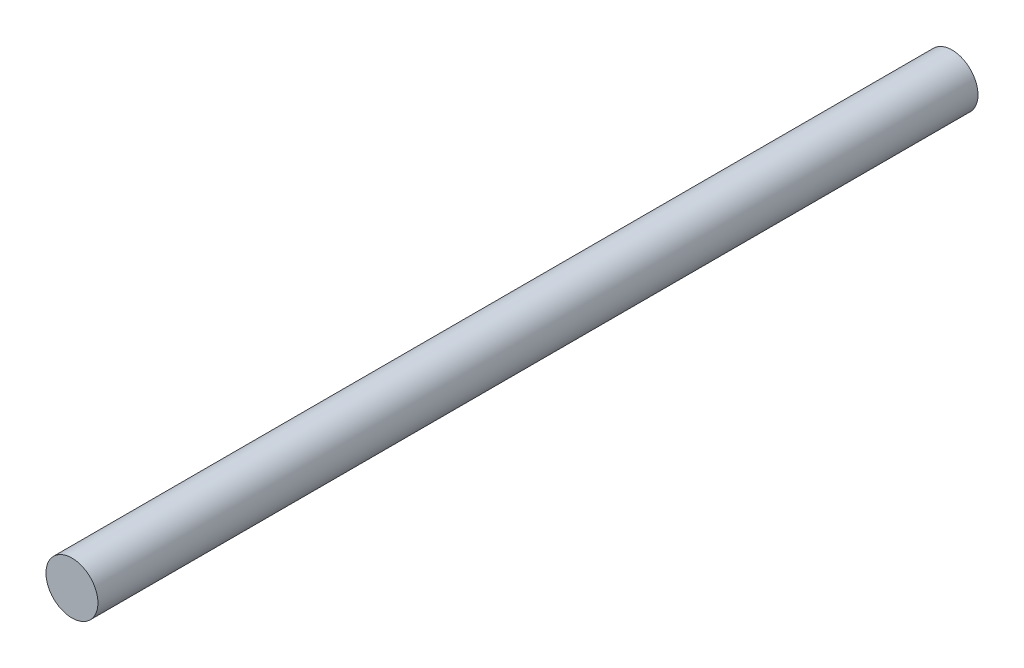
SolidWorks part; units mm, degrees
ref_plane "Front Plane" through (0, 0, 0) normal (0, 0, 1) x (1, 0, 0)
ref_plane "Top Plane" through (0, 0, 0) normal (0, 1, 0) x (1, 0, 0)
ref_plane "Right Plane" through (0, 0, 0) normal (1, 0, 0) x (0, 0, -1)
sketch "Sketch2" plane through (0, 0, 0) normal (0, 0, 1) x (1, 0, 0)
  circle A0 centre (0, 0) radius 3
  dimension "D1" = 6
extrude "Boss-Extrude1" add sketch "Sketch2" along normal blind 101.6
